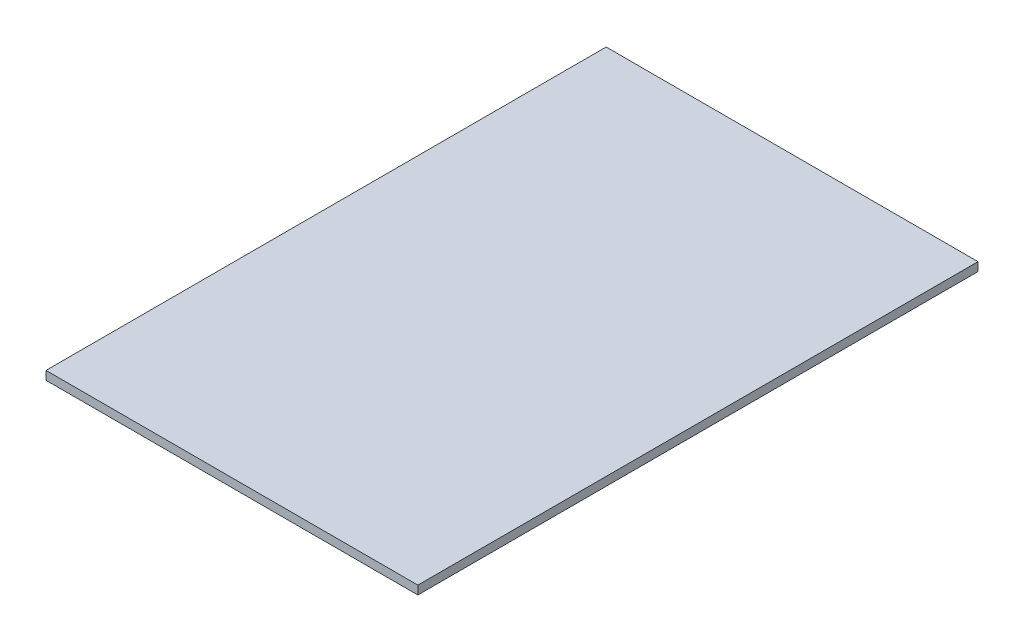
SolidWorks part; units mm, degrees
ref_plane "Front Plane" through (0, 0, 0) normal (0, 0, 1) x (1, 0, 0)
ref_plane "Top Plane" through (0, 0, 0) normal (0, 1, 0) x (1, 0, 0)
ref_plane "Right Plane" through (0, 0, 0) normal (1, 0, 0) x (0, 0, -1)
sketch "Sketch1" plane through (0, 0, 0) normal (0, 0, 1) x (1, 0, 0)
  line L1 (-305, 17) -> (431, 17)
  line L2 (-305, 17) -> (-305, 0)
  line L3 (-305, 0) -> (431, 0)
  line L4 (431, 17) -> (431, 0)
extrude "Boss-Extrude1" add sketch "Sketch1" against normal up to surface (1108.7 mm away)
